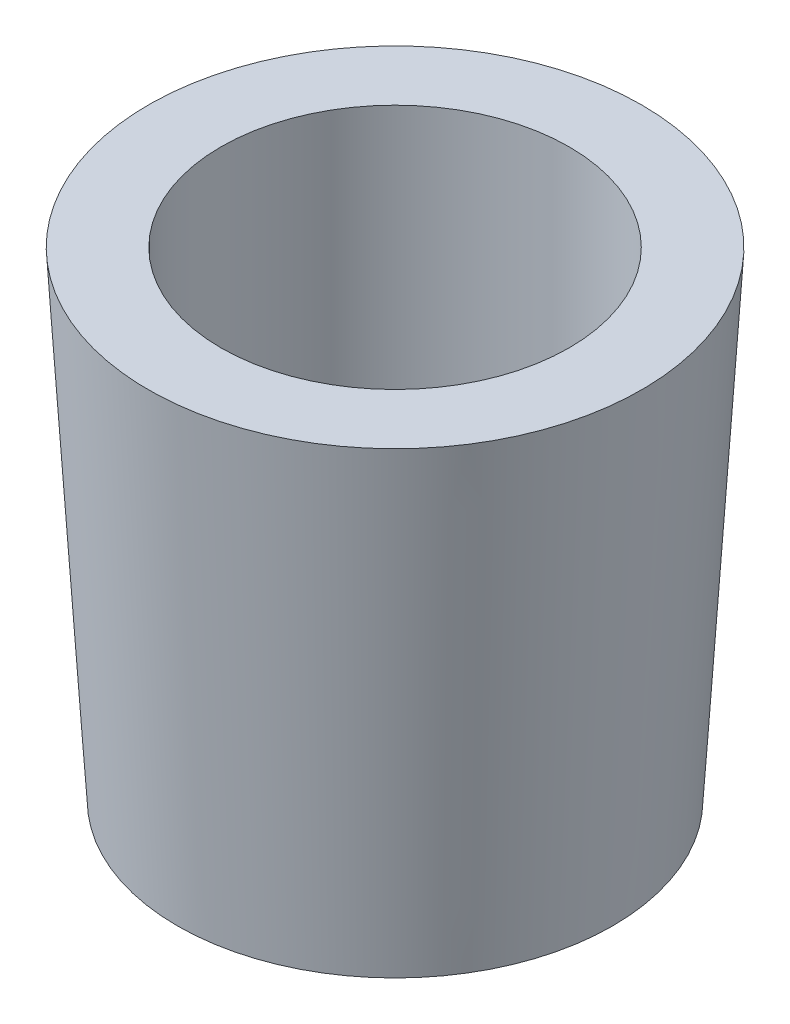
SolidWorks part; units mm, degrees
ref_plane "Plano frontal" through (0, 0, 0) normal (0, 0, 1) x (1, 0, 0)
ref_plane "Plano superior" through (0, 0, 0) normal (0, 1, 0) x (1, 0, 0)
ref_plane "Plano direito" through (0, 0, 0) normal (1, 0, 0) x (0, 0, -1)
sketch "Esboço1" plane through (0, 0, 0) normal (0, 0, 1) x (1, 0, 0)
  line L0 (0, 0) -> (0, 16.5)
  line L1 (0, 0) -> (7.5, 0)
  line L2 (0, 16.5) -> (8.5, 16.5)
  line L3 (8.5, 16.5) -> (7.5, 0)
  dimension "D1" = 16.5
  dimension "D2" = 7.5
  dimension "D3" = 8.5
revolve "Revolução1" add sketch "Esboço1" angle 360 about L0
sketch "Esboço2" plane through (0, 16.5, 0) normal (0, 1, 0) x (1, 0, 0)
  circle A0 centre (0, 0) radius 6
  dimension "D1" = 12
extrude "Corte-extrusão1" cut sketch "Esboço2" against normal blind 10
sketch "Esboço3" plane through (0, 0, 0) normal (0, -1, 0) x (1, 0, 0)
  circle A0 centre (0, 0) radius 5
  dimension "D1" = 10
extrude "Corte-extrusão2" cut sketch "Esboço3" against normal blind 4
